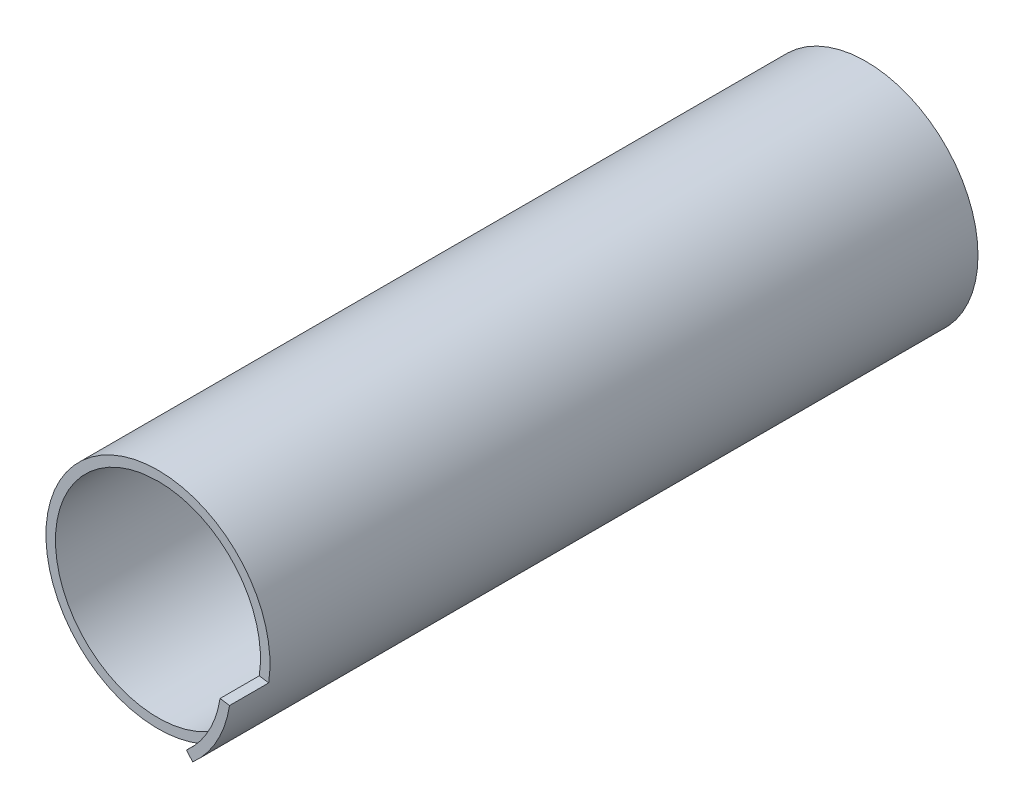
SolidWorks part; units mm, degrees
ref_plane "Спереди" through (0, 0, 0) normal (0, 0, 1) x (1, 0, 0)
ref_plane "Сверху" through (0, 0, 0) normal (0, 1, 0) x (1, 0, 0)
ref_plane "Справа" through (0, 0, 0) normal (1, 0, 0) x (0, 0, -1)
sketch "Эскиз2" plane through (0, 0, 0) normal (0, 0, 1) x (1, 0, 0)
  circle A0 centre (0, 0) radius 20
  circle A1 centre (0, 0) radius 18.3
  dimension "D1" = 40
  dimension "D2" = 36.6
extrude "Бобышка-Вытянуть1" add sketch "Эскиз2" along normal blind 126.4
sketch "Эскиз5" plane through (0, 0, 0) normal (0, 0, -1) x (-1, 0, 0)
  line L0 (0, 0) -> (0, 18.3) construction
  line L1 (0, 0) -> (2.9899, 18.0541) construction
  line L2 (0, 18.3) -> (0, 9.2195)
  line L3 (2.9899, 18.0541) -> (1.5063, 9.0957)
  circle A0 centre (0, 0) radius 18.3 construction
  arc A1 (0, 18.3) -> (2.9899, 18.0541) centre (0, 0) cw
  arc A2 (1.5063, 9.0957) -> (3.3753, 3.6888) centre (7.4257, 8.1154) ccw
  circle A3 centre (0, 0) radius 3
  arc A4 (-2.7273, 4.1907) -> (3.3753, 3.6888) centre (0, 0) ccw
  arc A5 (0, 9.2195) -> (-2.7273, 4.1907) centre (-6, 9.2195) cw
  point P16 (0, 5)
  dimension "D2" = 5
  dimension "D3" = 6
  dimension "D4" = 6
  dimension "D1" = 3
extrude "Бобышка-Вытянуть3" add sketch "Эскиз5" against normal through all
sketch "Sketch1" plane through (0, 0, 0) normal (0, 0, -1) x (-1, 0, 0)
  line L0 (0, 18.3) -> (2.9899, 18.0541)
  arc A0 (0, 18.3) -> (2.9899, 18.0541) centre (0, 0) ccw construction
  arc A2 (0, 18.3) -> (2.9899, 18.0541) centre (0, 0) ccw
extrude "Cut-Extrude1" cut sketch "Sketch1" against normal blind 59
sketch "Sketch2" plane through (0, 0, 126.4) normal (0, 0, 1) x (1, 0, 0)
  line L0 (0, 18.3) -> (-2.9899, 18.0541)
  arc A2 (0, 18.3) -> (-2.9899, 18.0541) centre (0, 0) cw
  arc A3 (-2.9899, 18.0541) -> (0, 18.3) centre (0, 0) ccw construction
extrude "Cut-Extrude2" cut sketch "Sketch2" against normal blind 59
sketch "Sketch3" plane through (0, 0, 0) normal (0, 0, 1) x (1, 0, 0)
  line L0 (5, 0) -> (5, 16.5617)
  line L1 (-5, 0) -> (-5, 16.5617)
  circle A0 centre (0, 0) radius 5 construction
  circle A1 centre (0, 0) radius 3
  arc A2 (5, 0) -> (-5, 0) centre (0, 0) cw
  arc A3 (5, 16.5617) -> (-5, 16.5617) centre (0, 0) ccw
  arc A4 (-2.9899, 18.0541) -> (0, 18.3) centre (0, 0) ccw construction
  dimension "D1" = 10
  dimension "D2" = 6
  dimension "D3" = 1
sketch "Sketch6" plane through (0, 0, 126.4) normal (0, 0, 1) x (1, 0, 0)
  line L0 (20, 0) -> (0, 0) construction
  line L2 (0, 0) -> (13.2053, -15.0207) construction
  line L3 (0, 0) -> (19.7709, -3.0183) construction
  line L4 (19.7709, -3.0183) -> (18.0904, -2.7618)
  line L5 (13.2053, -15.0207) -> (12.0828, -13.7439)
  circle A1 centre (0, 0) radius 20 construction
  arc A3 (19.7709, -3.0183) -> (13.2053, -15.0207) centre (0, 0) cw
  arc A5 (18.0904, -2.7618) -> (12.0828, -13.7439) centre (0, 0) cw
  arc A6 (-2.9899, 18.0541) -> (0, 18.3) centre (0, 0) ccw construction
  dimension "D1" = 40
  dimension "D2" = 48.68
extrude "Boss-Extrude4" add sketch "Sketch6" along normal blind 7
extrude "Boss-Extrude6" add sketch "Sketch3" along normal offset from surface (58.6 mm away) 0.4 separate body up to face at (-0.7271, 8.8405, 59)
